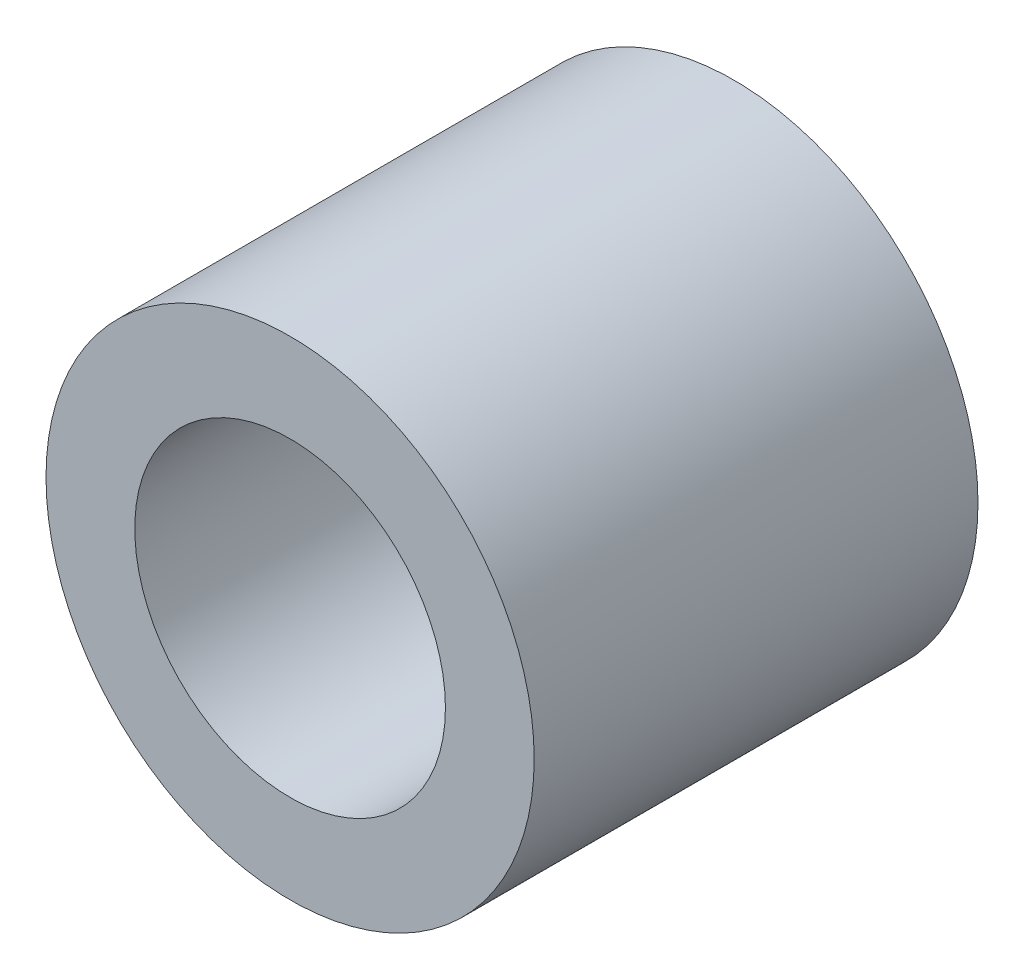
SolidWorks part; units mm, degrees
ref_plane "Płaszczyzna przednia" through (0, 0, 0) normal (0, 0, 1) x (1, 0, 0)
ref_plane "Płaszczyzna górna" through (0, 0, 0) normal (0, 1, 0) x (1, 0, 0)
ref_plane "Płaszczyzna prawa" through (0, 0, 0) normal (1, 0, 0) x (0, 0, -1)
sketch "Sketch1" plane through (0, 0, 0) normal (0, 0, 1) x (1, 0, 0)
  circle A0 centre (0, 0) radius 1.75
  circle A1 centre (0, 0) radius 2.75
  dimension "D1" = 3.5
  dimension "D2" = 5.5
extrude "Boss-Extrude1" add sketch "Sketch1" along normal blind 5
